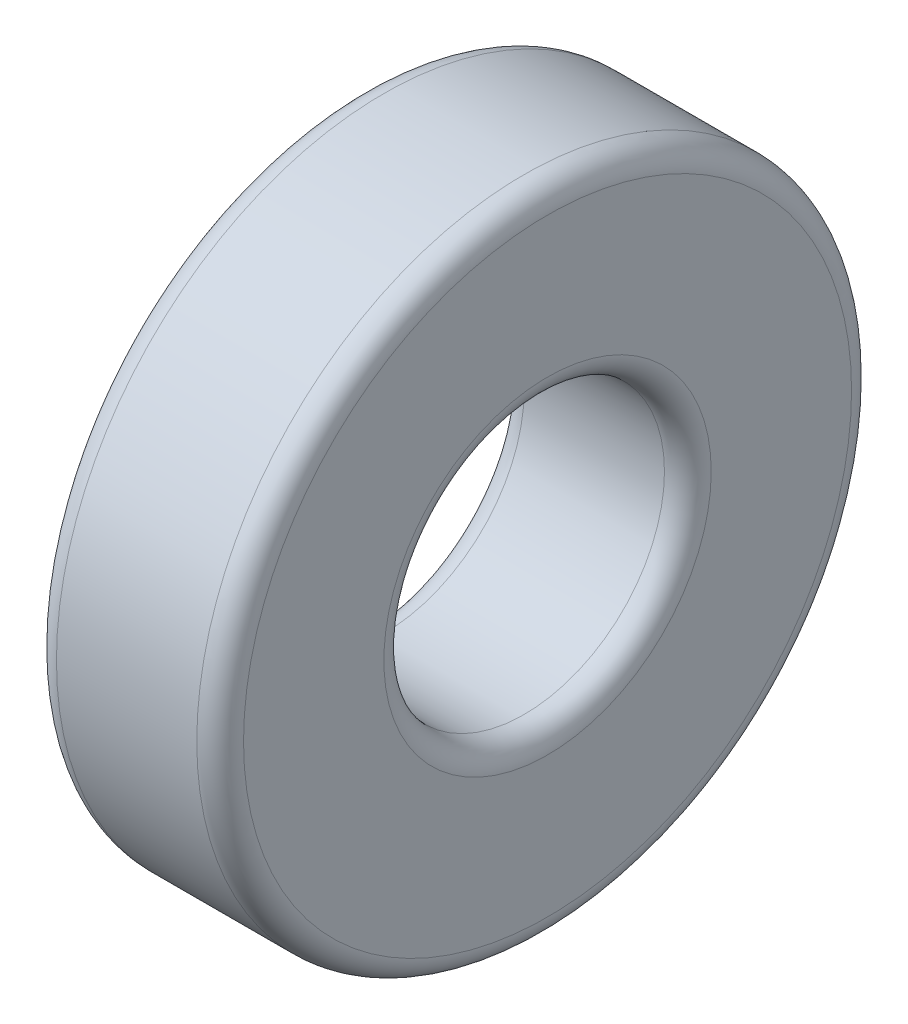
SolidWorks part; units mm, degrees
material "AISI 1020"
ref_plane "Спереди" through (0, 0, 0) normal (0, 0, 1) x (1, 0, 0)
ref_plane "Сверху" through (0, 0, 0) normal (0, 1, 0) x (1, 0, 0)
ref_plane "Справа" through (0, 0, 0) normal (1, 0, 0) x (0, 0, -1)
sketch "Эскиз1" plane through (0, 0, 0) normal (0, 0, 1) x (1, 0, 0)
  line L0 (0, 0) -> (-11.2148, 0) construction
  line L1 (0, 7) -> (0, 13)
  line L2 (-1, 14) -> (-7, 14)
  line L3 (-8, 13) -> (-8, 7)
  line L4 (-7, 6) -> (-1, 6)
  arc A0 (-7, 14) -> (-8, 13) centre (-7, 13) ccw
  arc A1 (0, 13) -> (-1, 14) centre (-1, 13) ccw
  arc A2 (0, 7) -> (-1, 6) centre (-1, 7) cw
  arc A3 (-8, 7) -> (-7, 6) centre (-7, 7) ccw
  point P9 (-8, 14)
  point P12 (0, 14)
  dimension "D4" = 1
  dimension "D1" = 12
  dimension "D2" = 28
  dimension "D3" = 8
revolve "Повернуть1" add sketch "Эскиз1" angle 360 about L0
